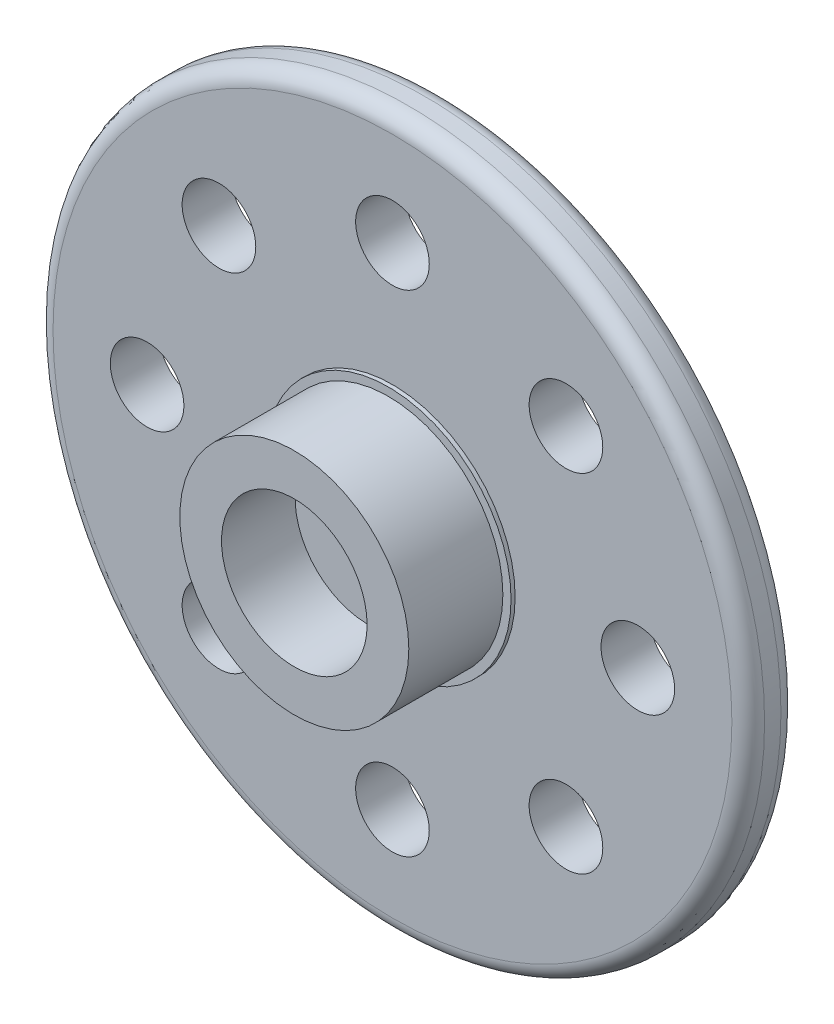
SolidWorks part; units mm, degrees
material "ABS"
ref_plane "Front Plane" through (0, 0, 0) normal (0, 0, 1) x (1, 0, 0)
ref_plane "Top Plane" through (0, 0, 0) normal (0, 1, 0) x (1, 0, 0)
ref_plane "Right Plane" through (0, 0, 0) normal (1, 0, 0) x (0, 0, -1)
sketch "Sketch1" plane through (0, 0, 0) normal (0, 0, 1) x (1, 0, 0)
  circle A0 centre (0, 0) radius 217.5
extrude "Boss-Extrude1" add sketch "Sketch1" along normal blind 30 contours A0
sketch "Sketch2" plane through (0, 0, 30) normal (0, 0, 1) x (1, 0, 0)
  circle A0 centre (0, 0) radius 75
extrude "Boss-Extrude2" add sketch "Sketch2" along normal blind 2.5 contours A0
sketch "Sketch3" plane through (0, 0, 32.5) normal (0, 0, 1) x (1, 0, 0)
  circle A0 centre (0, 0) radius 70
extrude "Boss-Extrude3" add sketch "Sketch3" along normal blind 57.5
sketch "Sketch12" plane through (0, 0, 30) normal (0, 0, 1) x (1, 0, 0)
  line L0 (150, 0) -> (106.066, 106.066) construction
  line L1 (106.066, 106.066) -> (0, 150) construction
  line L2 (0, 150) -> (-106.066, 106.066) construction
  line L3 (-106.066, 106.066) -> (-150, 0) construction
  line L4 (-150, 0) -> (-106.066, -106.066) construction
  line L5 (-106.066, -106.066) -> (0, -150) construction
  line L6 (0, -150) -> (106.066, -106.066) construction
  line L7 (106.066, -106.066) -> (150, 0) construction
  line L8 (150, 0) -> (-150, 0) construction
  line L9 (0, 150) -> (0, -150) construction
  circle A0 centre (0, 150) radius 22.5
  circle A1 centre (106.066, 106.066) radius 22.5
  circle A2 centre (150, 0) radius 22.5
  circle A3 centre (106.066, -106.066) radius 22.5
  circle A4 centre (0, -150) radius 22.5
  circle A5 centre (-106.066, -106.066) radius 22.5
  circle A6 centre (-150, 0) radius 22.5
  circle A7 centre (-106.066, 106.066) radius 22.5
  point P2 (0, 0)
  dimension "D1" = 300
  dimension "D3" = 45
  dimension "D2" = 135
extrude "Cut-Extrude2" cut sketch "Sketch12" against normal up to surface (30 mm away) up to face at (217.5, 0, 0)
fillet "Fillet2" radius 10 2 edges at (217.5, 0, 0) (217.5, 0, 30)
scale "Scale2" scale about centroid uniform scaling yes scale factor 0.1
sketch "Sketch14" plane through (0, 0, 30.0767) normal (0, 0, 1) x (1, 0, 0)
  circle A0 centre (0, 0) radius 4.45
  dimension "D1" = 8.9
extrude "Cut-Extrude3" cut sketch "Sketch14" against normal blind 4.5
